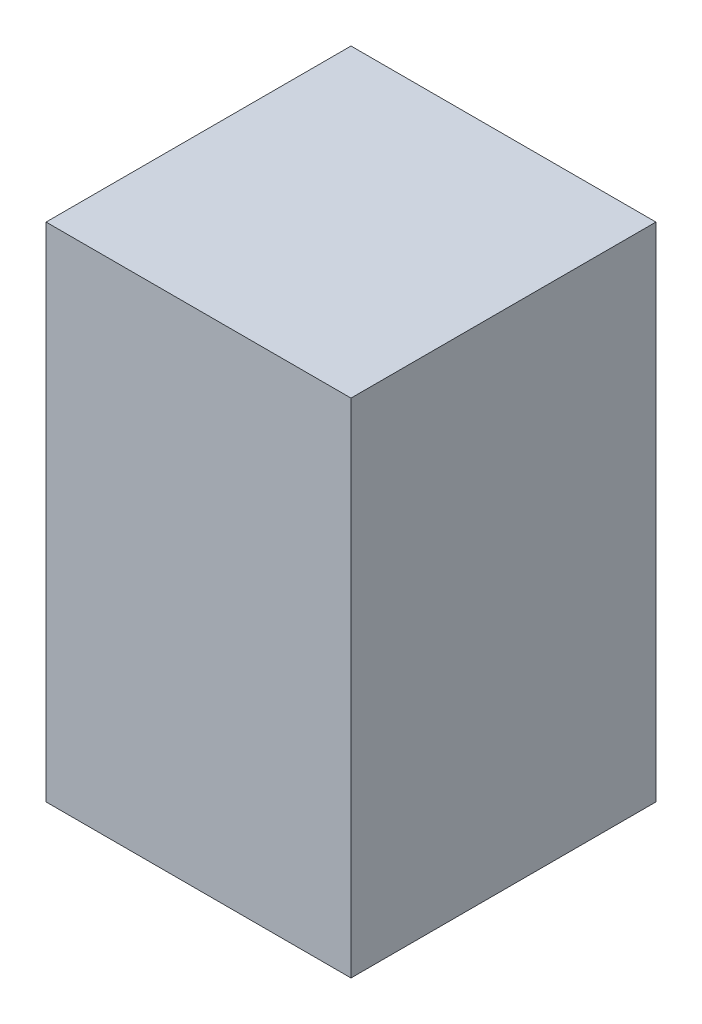
SolidWorks part; units mm, degrees
ref_plane "Front Plane" through (0, 0, 0) normal (0, 0, 1) x (1, 0, 0)
ref_plane "Top Plane" through (0, 0, 0) normal (0, 1, 0) x (1, 0, 0)
ref_plane "Right Plane" through (0, 0, 0) normal (1, 0, 0) x (0, 0, -1)
sketch "Sketch1" plane through (0, 0, 0) normal (0, 1, 0) x (1, 0, 0)
  line L1 (0, 0) -> (86.36, 0)
  line L2 (0, 0) -> (0, 86.36)
  line L3 (0, 86.36) -> (86.36, 86.36)
  line L4 (86.36, 0) -> (86.36, 86.36)
  dimension "D1" = 86.36
  dimension "D2" = 86.36
extrude "Extrude1" add sketch "Sketch1" along normal blind 142.24
